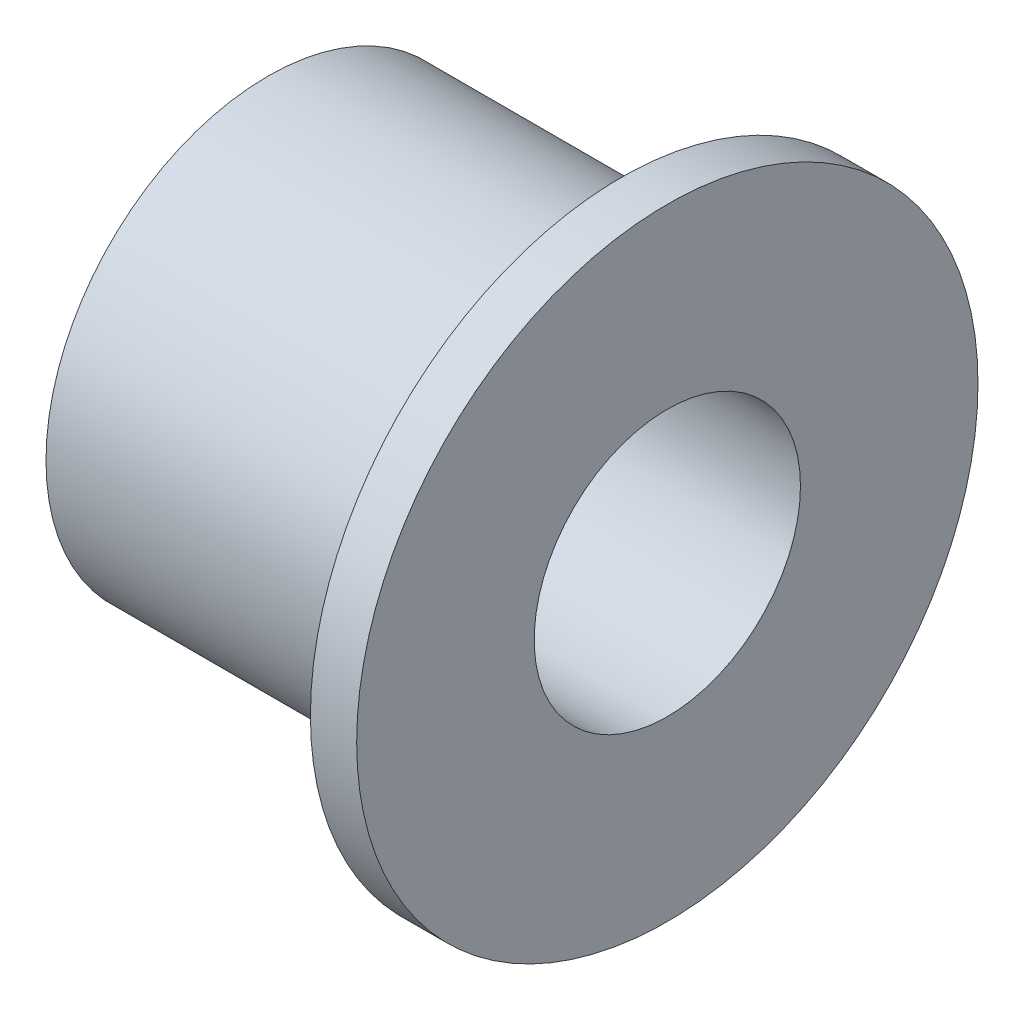
SolidWorks part; units mm, degrees
material "Aluminum Bronze"
ref_plane "Front Plane" through (0, 0, 0) normal (0, 0, 1) x (1, 0, 0)
ref_plane "Top Plane" through (0, 0, 0) normal (0, 1, 0) x (1, 0, 0)
ref_plane "Right Plane" through (0, 0, 0) normal (1, 0, 0) x (0, 0, -1)
sketch "Sketch1" plane through (0, 0, 0) normal (1, 0, 0) x (0, 0, -1)
  circle A0 centre (0, 0) radius 4.7625
  circle A1 centre (0, 0) radius 7.9375
  dimension "D1" = 9.525
  dimension "D2" = 15.875
extrude "Boss-Extrude1" add sketch "Sketch1" along normal blind 12.7
sketch "Sketch2" plane through (12.7, 0, 0) normal (1, 0, 0) x (0, 0, -1)
  circle A0 centre (0, 0) radius 11.1125
  circle A1 centre (0, 0) radius 4.7625 construction
  circle A2 centre (0, 0) radius 4.7625
  dimension "D1" = 22.225
extrude "Boss-Extrude2" add sketch "Sketch2" along normal blind 1.5875 and the other way blind 0.0672
